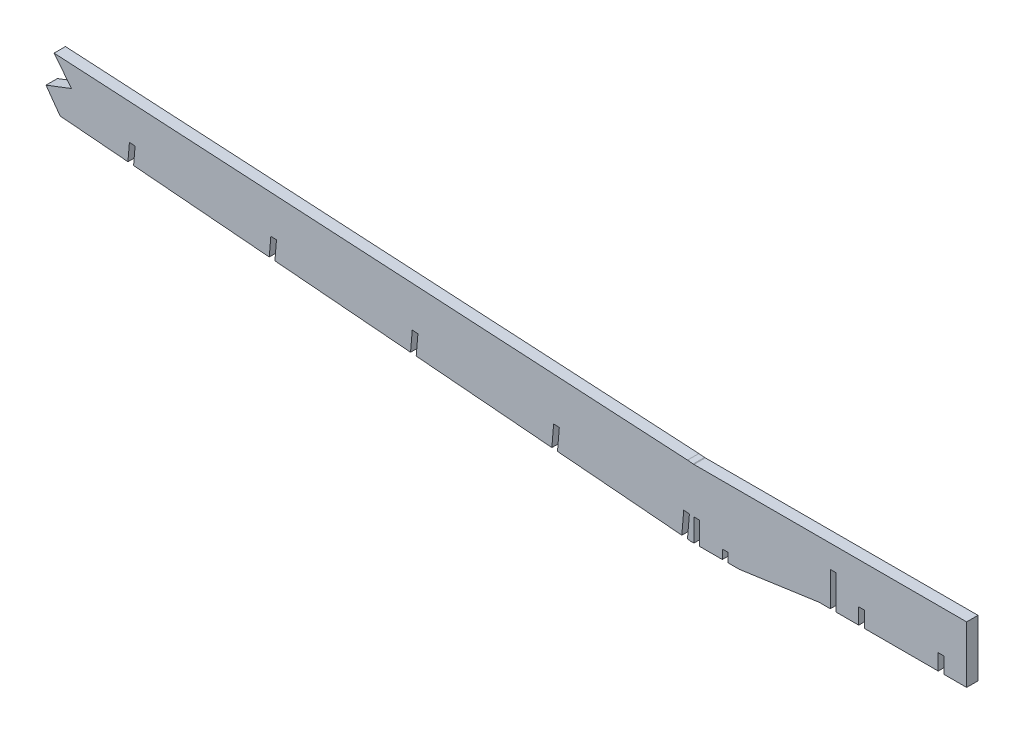
SolidWorks part; units mm, degrees
material "Balsa"
ref_plane "Front Plane" through (0, 0, 0) normal (0, 0, 1) x (1, 0, 0)
ref_plane "Top Plane" through (0, 0, 0) normal (0, 1, 0) x (1, 0, 0)
ref_plane "Right Plane" through (0, 0, 0) normal (1, 0, 0) x (0, 0, -1)
sketch "Sketch1" plane through (0, 0, 0) normal (0, 0, 1) x (1, 0, 0)
  line L0 (76.2, 56.7475) -> (76.2, 37.6975)
  line L1 (79.375, 56.7475) -> (79.375, 37.6975)
  line L2 (0, 44.0475) -> (0, 31.3475)
  line L3 (3.175, 44.0475) -> (3.175, 31.3475)
  line L4 (-5.7133, 44.4467) -> (-6.776, 31.7912)
  line L5 (-2.5494, 44.181) -> (-3.6121, 31.5255)
  line L6 (-1.4923, 31.3475) -> (25.4, 31.3475)
  line L7 (25.4, 31.3475) -> (69.85, 37.6975)
  line L8 (-2.5494, 44.181) -> (-0.424, 69.4919) construction
  line L9 (-0.424, 69.4919) -> (-3.5879, 69.7576)
  line L10 (-3.5879, 69.7576) -> (-5.7133, 44.4467) construction
  line L11 (-5.7133, 44.4467) -> (-2.5494, 44.181)
  line L12 (3.175, 44.0475) -> (3.175, 69.4475) construction
  line L13 (3.175, 69.4475) -> (0, 69.4475)
  line L14 (0, 69.4475) -> (0, 44.0475) construction
  line L15 (0, 44.0475) -> (3.175, 44.0475)
  line L16 (92.075, 37.6975) -> (92.075, 46.5875)
  line L17 (-942.8808, 122.7744) -> (-947.5199, 67.5279)
  line L18 (0, 69.4475) -> (-0.424, 69.4919)
  line L19 (3.175, 69.4475) -> (152.4, 69.4475)
  line L20 (152.4, 69.4475) -> (152.4, 37.6975)
  line L21 (152.4, 37.6975) -> (69.85, 37.6975)
  line L22 (92.075, 46.5875) -> (95.25, 46.5875)
  line L23 (95.25, 46.5875) -> (95.25, 37.6975)
  line L24 (-1.4923, 31.3475) -> (-943.9128, 110.4848)
  line L25 (79.375, 69.4475) -> (79.375, 56.7475)
  line L26 (-942.8808, 122.7744) -> (-3.5879, 69.7576)
  line L27 (136.525, 37.6975) -> (136.525, 46.5875)
  line L28 (76.2, 69.4475) -> (76.2, 56.7475)
  line L29 (79.375, 56.7475) -> (76.2, 56.7475)
  line L30 (-943.5688, 114.5813) -> (-5.7133, 44.4467)
  line L31 (136.525, 46.5875) -> (139.7, 46.5875)
  line L32 (139.7, 46.5875) -> (139.7, 37.6975)
  line L33 (15.875, 31.3475) -> (15.875, 36.4275)
  line L34 (15.875, 36.4275) -> (19.05, 36.4275)
  line L35 (19.05, 36.4275) -> (19.05, 31.3475)
  line L36 (-942.8808, 122.7744) -> (-946.0519, 122.9534)
  line L37 (-946.0519, 122.9534) -> (-946.5835, 116.6233)
  line L38 (-946.5835, 116.6233) -> (-943.4123, 116.4443)
  dimension "D3" = 76.2
  dimension "D10" = 12.3329
  dimension "D11" = 8.2219
  dimension "D2" = 25.4
  dimension "D4" = 25.4
  dimension "D5" = 12.7
  dimension "D7" = 3.175
  dimension "D9" = 3.175
  dimension "D12" = 3.175
  dimension "D6" = 19.05
  dimension "D13" = 6.35
  dimension "D14" = 12.7
  dimension "D16" = 3.175
  dimension "D17" = 3.175
  dimension "D18" = 12.7
  dimension "D19" = 12.7
  dimension "D20" = 8.89
  dimension "D21" = 8.89
  dimension "D15" = 76.2
  dimension "D22" = 12.7
  dimension "D23" = 3.175
  dimension "D24" = 5.08
  dimension "D8" = 6.35
  dimension "D25" = 3.175
  dimension "D26" = 6.35
extrude "Boss-Extrude1" add sketch "Sketch1" along normal mid plane 6.35 contours L17 L30 L11 L5 L24 L6 L2 L15 L3 L7 L21 L0 L28 L19 L13 L18 L9 L26 | L30 L17 L24 L4 | L29 L25 L19 L28 | L19 L25 L1 L21 L20 | L37 L38 L17 L36
sketch "Sketch2" plane through (0, 0, 3.175) normal (0, 0, 1) x (1, 0, 0)
  line L2 (-73.2652, 73.2231) -> (-80.3969, -11.7061)
  line L3 (-943.5688, 114.5813) -> (-5.7133, 44.4467)
  line L6 (-76.4291, 73.4888) -> (-83.5608, -11.4404)
  line L7 (-6.776, 31.7912) -> (-943.9128, 110.4848)
  line L10 (-152.4177, 77.6821) -> (-159.3225, -4.5442)
  line L14 (-155.5816, 77.9478) -> (-162.4863, -4.2785)
  line L18 (-231.5658, 82.1932) -> (-238.251, 2.5812)
  line L22 (-234.7297, 82.4589) -> (-241.4149, 2.8469)
  line L26 (-310.7178, 86.6582) -> (-317.1769, 9.7387)
  line L30 (-313.8817, 86.9239) -> (-320.3408, 10.0043)
  line L34 (-389.8657, 91.1713) -> (-396.1056, 16.8623)
  line L38 (-393.0296, 91.437) -> (-399.2695, 17.128)
  line L42 (-469.0186, 95.6263) -> (-475.031, 24.0265)
  line L46 (-472.1824, 95.892) -> (-478.1948, 24.2921)
  line L50 (-548.1666, 100.1381) -> (-553.9596, 31.1506)
  line L54 (-551.3305, 100.4038) -> (-557.1235, 31.4163)
  line L58 (-627.3195, 104.5918) -> (-632.8849, 38.3152)
  line L62 (-630.4834, 104.8575) -> (-636.0488, 38.5809)
  line L66 (-706.4673, 109.1069) -> (-711.8138, 45.4365)
  line L70 (-709.6312, 109.3725) -> (-714.9777, 45.7022)
  line L74 (-785.6206, 113.5558) -> (-790.7389, 52.6041)
  line L78 (-788.7845, 113.8214) -> (-793.9027, 52.8697)
  line L82 (-864.7684, 118.071) -> (-869.6679, 59.7246)
  line L86 (-867.9323, 118.3366) -> (-872.8317, 59.9902)
  line L89 (-942.9091, 122.4365) -> (-947.5795, 66.8182)
  line M2 (-943.9128, 110.4848) -> (-6.776, 31.7912)
extrude "Cut-Extrude1" cut sketch "Sketch2" against normal through all contours L3 L6 L2 M2 | L3 L14 L7 L10 | L3 L22 L7 L18 | L3 L30 L7 L26 | L3 L38 L7 L34 | L3 L46 L7 L42 | L3 L54 L7 L50 | L3 L62 L7 L58 | L3 L70 L7 L66 | L3 L78 L7 L74 | L3 L86 L7 L82
sketch "Sketch3" plane through (0, 0, 3.175) normal (0, 0, 1) x (1, 0, 0)
  line L0 (-354.2316, 60.9679) -> (-362.1267, 71.9794)
  line L1 (-316.3285, 57.7851) -> (-392.1347, 64.1507) construction
  line L2 (-362.1267, 71.9794) -> (-347.8724, 77.4491)
  line L3 (-347.8724, 77.4491) -> (-357.599, 89.7392)
  line L4 (-946.0519, 122.9534) -> (-3.5879, 69.7576) construction
  line L5 (-357.599, 89.7392) -> (-993.7912, 254.1833)
  line L6 (-993.7912, 254.1833) -> (-993.7912, 28.7351)
  line L7 (-993.7912, 28.7351) -> (-354.2316, 60.9679)
extrude "Cut-Extrude2" cut sketch "Sketch3" against normal blind 7.62
equation "\"D11@Sketch1\"=\"D10@Sketch1\"*(2/3)"
